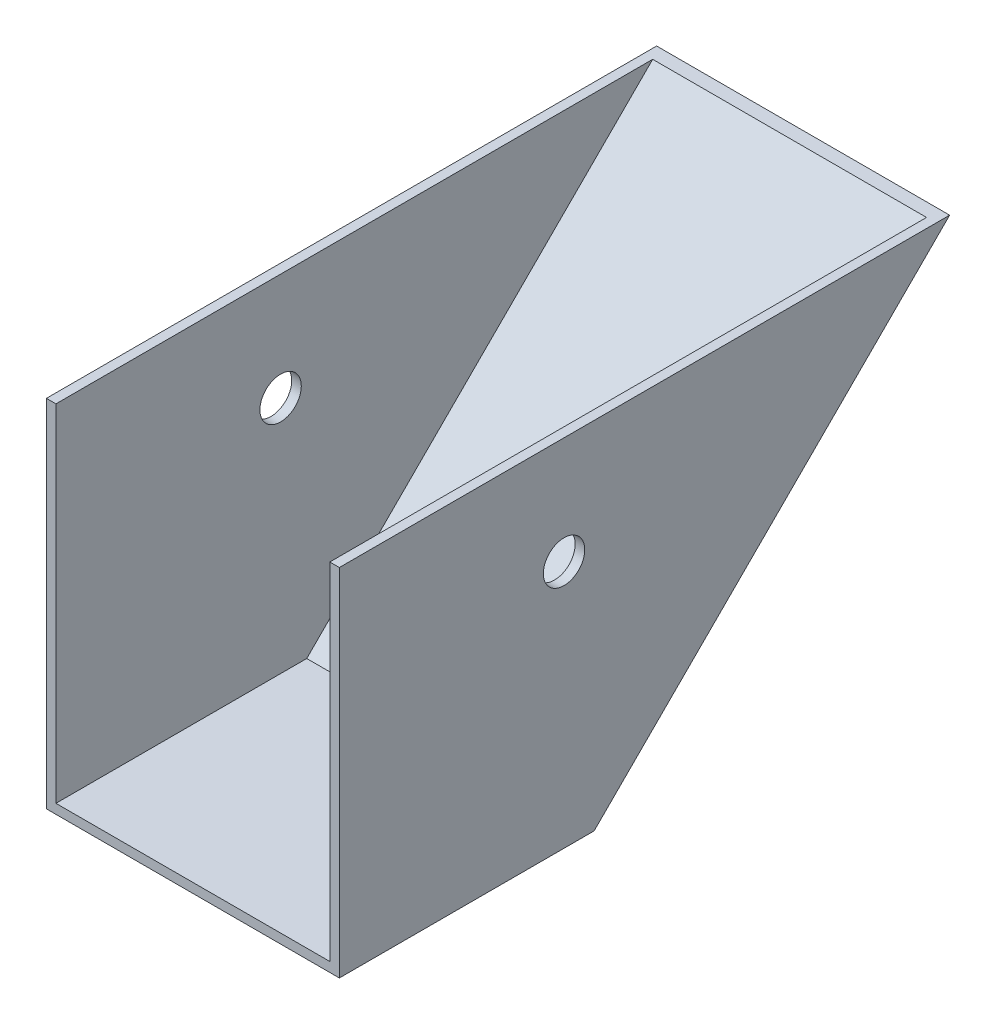
SolidWorks part; units mm, degrees
material "ALUMINUM 6061-T6"
ref_plane "Front Plane" through (0, 0, 0) normal (0, 0, 1) x (1, 0, 0)
ref_plane "Top Plane" through (0, 0, 0) normal (0, 1, 0) x (1, 0, 0)
ref_plane "Right Plane" through (0, 0, 0) normal (1, 0, 0) x (0, 0, -1)
sketch "Sketch2" plane through (0, 0, 0) normal (0, 1, 0) x (1, 0, 0)
  line L1 (-146.05, -317.5) -> (146.05, -317.5)
  line L2 (-146.05, -317.5) -> (-146.05, 317.5)
  line L3 (-146.05, 317.5) -> (146.05, 317.5)
  line L4 (146.05, -317.5) -> (146.05, 317.5)
  line L5 (-146.05, -317.5) -> (146.05, 317.5) construction
  line L6 (-146.05, 317.5) -> (146.05, -317.5) construction
  point P0 (0, 0)
extrude "Boss-Extrude1" add sketch "Sketch2" along normal mid plane 381
sketch "Sketch4" plane through (-146.05, 0, 0) normal (-1, 0, 0) x (0, 0, 1)
  line L0 (-317.5, 190.5) -> (63.5, -190.5)
  line L1 (-317.5, -190.5) -> (317.5, -190.5) construction
  line L2 (-317.5, 190.5) -> (-317.5, -190.5) construction
  line L3 (-317.5, 190.5) -> (-317.5, -190.5)
  line L4 (-317.5, -190.5) -> (63.5, -190.5)
  dimension "D1" = 45
extrude "Cut-Extrude2" cut sketch "Sketch4" against normal blind 381
shell "Shell1" thickness 9.525
sketch "Sketch5" plane through (0, 190.5, 0) normal (0, 1, 0) x (1, 0, 0)
  line L1 (-146.05, 317.5) -> (146.05, 317.5)
  line L2 (-146.05, 317.5) -> (-146.05, -317.5)
  line L3 (-146.05, -317.5) -> (146.05, -317.5)
  line L4 (146.05, 317.5) -> (146.05, -317.5)
extrude "Cut-Extrude3" cut sketch "Sketch5" against normal blind 24.892
sketch "Sketch6" plane through (-146.05, 0, 0) normal (-1, 0, 0) x (0, 0, 1)
  circle A0 centre (93.5173, 56.9612) radius 20.6375
  dimension "D1" = 41.275
extrude "Cut-Extrude4" cut sketch "Sketch6" against normal blind 514.096
sketch "Sketch10" plane through (0, 165.608, 0) normal (0, 1, 0) x (1, 0, 0)
  line L1 (-146.05, 292.608) -> (146.05, 292.608)
  line L2 (-146.05, 292.608) -> (-146.05, -317.5)
  line L3 (-146.05, -317.5) -> (146.05, -317.5)
  line L4 (146.05, 292.608) -> (146.05, -317.5)
extrude "Cut-Extrude7" cut sketch "Sketch10" against normal blind 1.6933
